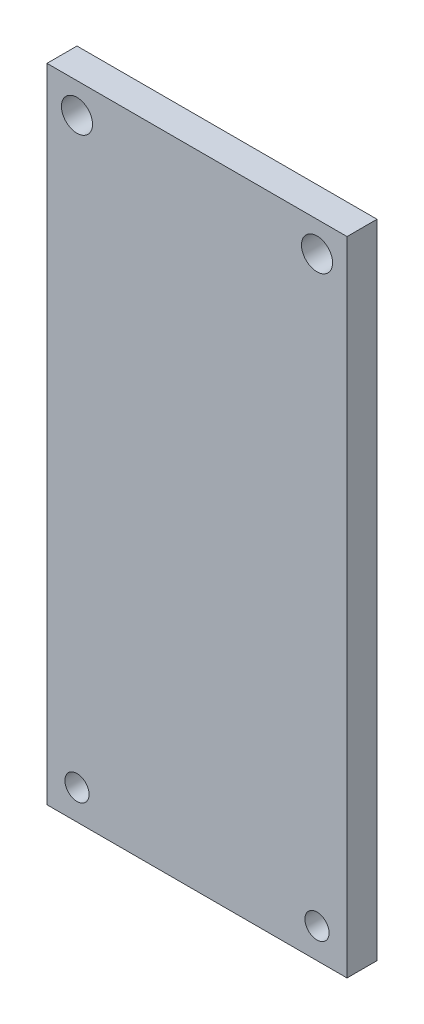
SolidWorks part; units mm, degrees
ref_plane "前视基准面" through (0, 0, 0) normal (0, 0, 1) x (1, 0, 0)
ref_plane "上视基准面" through (0, 0, 0) normal (0, 1, 0) x (1, 0, 0)
ref_plane "右视基准面" through (0, 0, 0) normal (1, 0, 0) x (0, 0, -1)
sketch "草图1" plane through (0, 0, 0) normal (0, 0, 1) x (1, 0, 0)
  line L0 (7.5789, 48.7) -> (7.5789, -15.5) construction
  line L1 (-7.4211, 48.7) -> (22.5789, 48.7)
  line L2 (-7.4211, 48.7) -> (-7.4211, -15.5)
  line L3 (-7.4211, -15.5) -> (22.5789, -15.5)
  line L4 (22.5789, 48.7) -> (22.5789, -15.5)
  circle A0 centre (-4.4211, 45.7) radius 1.5542
  circle A1 centre (-4.4211, -12.5) radius 1.2117
  circle A2 centre (19.5789, -12.5) radius 1.2117
  circle A3 centre (19.5789, 45.7) radius 1.5542
  dimension "D1" = 3
  dimension "D3" = 3
  dimension "D4" = 3
  dimension "D5" = 12
  dimension "D6" = 58.2
  dimension "D2" = 3
extrude "凸台-拉伸1" add sketch "草图1" along normal blind 3
